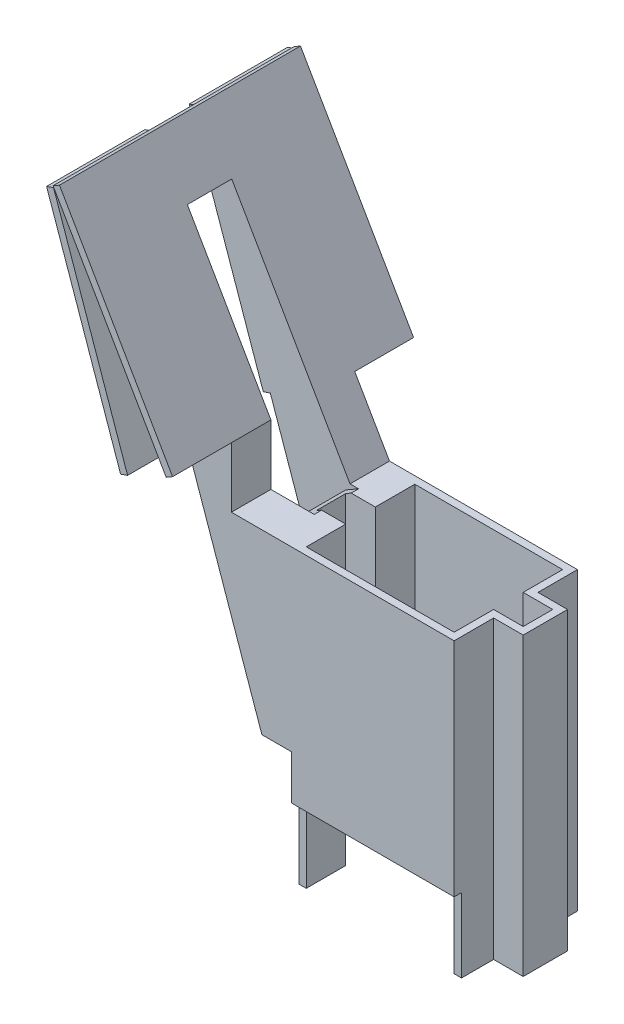
SolidWorks part; units mm, degrees
ref_plane "Ebene vorne" through (0, 0, 0) normal (0, 0, 1) x (1, 0, 0)
ref_plane "Ebene oben" through (0, 0, 0) normal (0, 1, 0) x (1, 0, 0)
ref_plane "Ebene rechts" through (0, 0, 0) normal (1, 0, 0) x (0, 0, -1)
sketch "Skizze1" plane through (0, 0, 0) normal (0, 1, 0) x (1, 0, 0)
  line L0 (-5, 1) -> (-5, 3.67)
  line L1 (5, -3.67) -> (-5, -3.67)
  line L2 (5, -3.67) -> (5, -1)
  line L3 (5, 3.67) -> (-5, 3.67)
  line L4 (-5, -3.67) -> (-5, -1)
  line L5 (5, -3.67) -> (-5, 3.67) construction
  line L6 (5, 3.67) -> (-5, -3.67) construction
  line L7 (7, -1) -> (5, -1)
  line L8 (7, -1) -> (7, 1)
  line L9 (7, 1) -> (5, 1)
  line L10 (-7, -1) -> (-7, 1)
  line L11 (7, -1) -> (-7, 1) construction
  line L12 (7, 1) -> (-7, -1) construction
  line L13 (5.5, -4.17) -> (-5.5, -4.17)
  line L14 (7.5, -1.5) -> (7.5, 1.5)
  line L15 (5.5, 4.17) -> (-5.5, 4.17)
  line L16 (-7.5, -1.5) -> (-7.5, 1.5)
  line L17 (5.5, -2.87) -> (-5.5, 2.87) construction
  line L18 (5.5, 3.21) -> (-5.5, -3.21) construction
  line L19 (-5, 1) -> (-7, 1)
  line L20 (5, 1) -> (5, 3.67)
  line L21 (-5, -1) -> (-7, -1)
  line L25 (-7.5, 1.5) -> (-5.5, 1.5)
  line L26 (-5.5, 4.17) -> (-5.5, 1.5)
  line L29 (7.5, 1.5) -> (5.5, 1.5)
  line L30 (5.5, 4.17) -> (5.5, 1.5)
  line L33 (7.5, -1.5) -> (5.5, -1.5)
  line L34 (5.5, -4.17) -> (5.5, -1.5)
  line L37 (-7.5, -1.5) -> (-5.5, -1.5)
  line L38 (-5.5, -4.17) -> (-5.5, -1.5)
  point P0 (0, 0)
  point P5 (0, 0)
  point P11 (0, 0)
  dimension "D1" = 10
  dimension "D2" = 2
  dimension "D3" = 14
  dimension "D4" = 0.5
  dimension "D5" = 0.5
  dimension "D6" = 7.34
  dimension "D7" = 0.5
  dimension "D8" = 0.5
  dimension "D9" = 0.5
  dimension "D10" = 0.5
  dimension "D11" = 0.5
  dimension "D12" = 0.5
extrude "Aufsatz-Linear austragen1" add sketch "Skizze1" along normal blind 20
sketch "Skizze8" plane through (0, 0, 3.67) normal (0, 0, -1) x (-1, 0, 0)
  line L0 (5.5, 20) -> (5.5, 0) construction
  line L1 (-5.5, 0) -> (5.5, 0)
  line L2 (-5.5, 0) -> (-5.5, 5)
  line L3 (-5.5, 5) -> (5.5, 5)
  line L4 (5.5, 0) -> (5.5, 5)
  dimension "D1" = 5
extrude "Schnitt-Linear austragen2" cut sketch "Skizze8" against normal up to next
sketch "Skizze10" plane through (0, 0, -4.17) normal (0, 0, -1) x (-1, 0, 0)
  line L1 (5.5, 20) -> (7.2113, 20)
  line L2 (5.5, 20) -> (5.5, 19.5)
  line L3 (5.5, 19.5) -> (7.5, 19.5)
  line L5 (7.5, 19.5) -> (17.6443, 37.0705)
  line L6 (17.6443, 37.0705) -> (17.2113, 37.3205)
  line L7 (17.2113, 37.3205) -> (7.2113, 20)
  line L8 (7.5, 20) -> (7.5, 0) construction
  dimension "D1" = 0.5
  dimension "D2" = 0.5
  dimension "D3" = 150
  dimension "D4" = 20
extrude "Aufsatz-Linear austragen3" add sketch "Skizze10" against normal up to vertex (8.34 mm away) up to point (-5.5, 20, 4.17)
sketch "Skizze12" plane through (0, 19.5, 0) normal (0, -1, 0) x (1, 0, 0)
  line L1 (-7, -1) -> (-5.5, -1)
  line L2 (-7, -1) -> (-7, 1)
  line L3 (-7, 1) -> (-5.5, 1)
  line L4 (-5.5, -1) -> (-5.5, 1)
extrude "Schnitt-Linear austragen3" cut sketch "Skizze12" against normal up to next
sketch "Skizze13" plane through (0, 0, -4.17) normal (0, 0, -1) x (-1, 0, 0)
  line L0 (17.2113, 37.3205) -> (9.5613, 24.0703)
  line L1 (17.2113, 37.3205) -> (7.2113, 20) construction
  line L2 (9.5613, 24.0703) -> (9.9943, 23.8203)
  line L3 (7.5, 19.5) -> (17.6443, 37.0705) construction
  line L4 (9.9943, 23.8203) -> (17.6443, 37.0705)
  line L5 (17.6443, 37.0705) -> (17.2113, 37.3205)
  dimension "D1" = 15.3
extrude "Aufsatz-Linear austragen4" add sketch "Skizze13" along normal blind 3.98
sketch "Skizze15" plane through (0, 0, -1.5) normal (0, 0, -1) x (-1, 0, 0)
  line L4 (5.5, 8) -> (5.5, 19.5)
  line L5 (5.5, 19.5) -> (7.5, 19.5)
  line L6 (7.5, 19.5) -> (17.6443, 37.0705)
  line L14 (17.6443, 37.0705) -> (7.5, 8)
  line L15 (7.5, 19.5) -> (7.5, 0) construction
  line L16 (7.5, 8) -> (5.5, 8)
  line L17 (5.5, 0) -> (7.5, 0) construction
  dimension "D1" = 8
extrude "Aufsatz-Linear austragen5" add sketch "Skizze15" along normal up to vertex
mirror "Spiegeln1" about plane through (0, 0, 0) normal (0, 0, 1) of "Aufsatz-Linear austragen4"
sketch "Skizze16" plane through (0, 0, 1.5) normal (0, 0, 1) x (1, 0, 0)
  line L0 (-17.6443, 37.0705) -> (-7.5, 8)
  line L1 (-7.5, 8) -> (-5.5, 8)
  line L2 (-5.5, 19.5) -> (-5.5, 5) construction
  line L3 (-5.5, 8) -> (-5.5, 19.5)
  line L4 (-5.5, 19.5) -> (-7.5, 19.5)
  line L5 (-7.5, 19.5) -> (-17.6443, 37.0705)
extrude "Aufsatz-Linear austragen6" add sketch "Skizze16" along normal up to vertex
sketch "Skizze17" plane through (2.8187, 1.6274, 0) normal (-0.866, -0.5, 0) x (0, 0, 1)
  line L0 (1.5, 40.9262) -> (1.5, 10.6782) construction
  line L1 (-1.5, 20.6375) -> (1.5, 20.6375)
  line L2 (-1.5, 20.6375) -> (-1.5, 36.9262)
  line L3 (-1.5, 36.9262) -> (1.5, 36.9262)
  line L4 (1.5, 20.6375) -> (1.5, 36.9262)
  line L6 (1.5, 40.9262) -> (-1.5, 40.9262) construction
  dimension "D1" = 4
extrude "Schnitt-Linear austragen4" cut sketch "Skizze17" against normal up to next
sketch "Skizze22" plane through (0, 0, -1.5) normal (0, 0, 1) x (1, 0, 0)
  line L0 (-17.6114, 36.9761) -> (-12.6034, 22.6248)
  line L1 (-17.6443, 37.0705) -> (-7.5, 8) construction
  line L2 (-12.6034, 22.6248) -> (-13.0755, 22.46)
  line L3 (-13.0755, 22.46) -> (-18.0835, 36.8114)
  line L4 (-18.0835, 36.8114) -> (-17.6114, 36.9761)
  dimension "D1" = 15.2
  dimension "D2" = 0.5
  dimension "D3" = 0.1
extrude "Aufsatz-Linear austragen15" add sketch "Skizze22" against normal blind 6.65
mirror "Spiegeln2" about plane through (0, 0, 0) normal (0, 0, 1) of "Aufsatz-Linear austragen15"
sketch "Skizze23" plane through (0, 0, 4.17) normal (0, 0, 1) x (1, 0, 0)
  line L0 (-7.2113, 20) -> (-9.5613, 20)
  line L1 (-9.5613, 20) -> (-9.5613, 24.0703)
  line L3 (-7.2113, 20) -> (-9.5613, 24.0703)
  line L4 (-9.5613, 24.0703) -> (-7.2113, 20) construction
  point P3 (-9.5613, 24.0703)
extrude "Schnitt-Linear austragen5" cut sketch "Skizze23" against normal up to next
